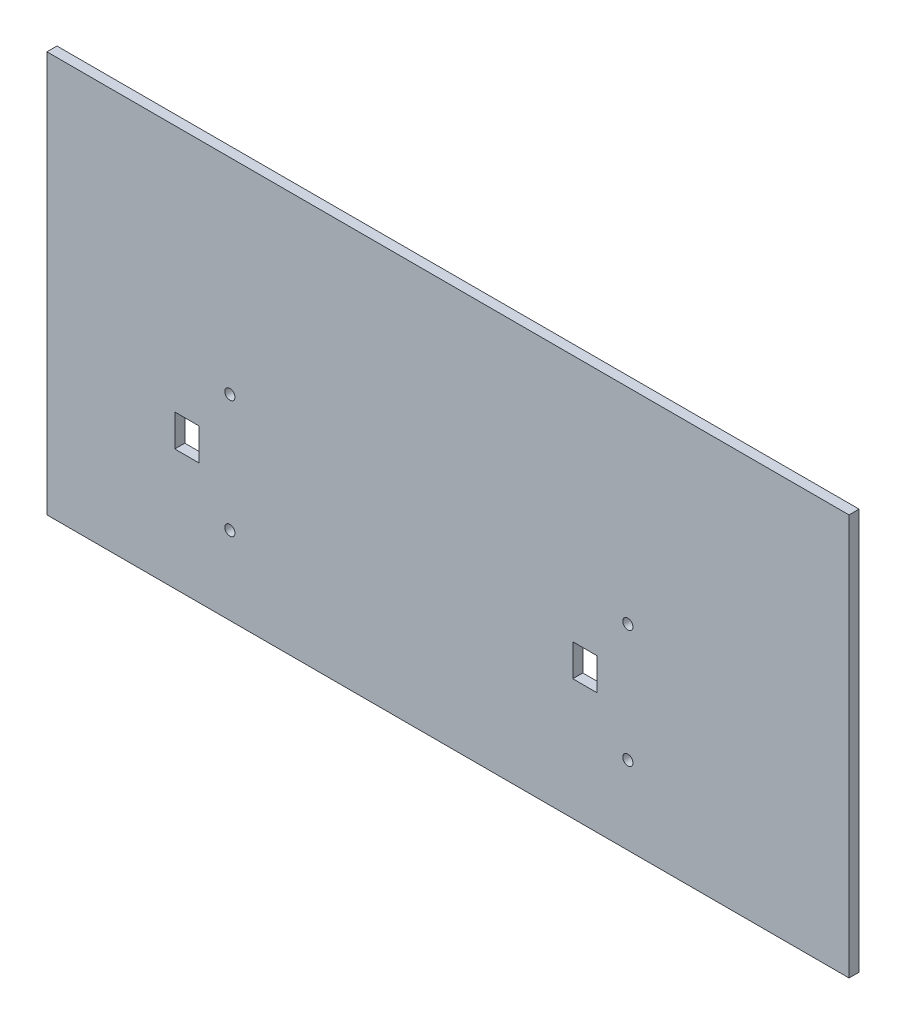
SolidWorks part; units mm, degrees
ref_plane "Front Plane" through (0, 0, 0) normal (0, 0, 1) x (1, 0, 0)
ref_plane "Top Plane" through (0, 0, 0) normal (0, 1, 0) x (1, 0, 0)
ref_plane "Right Plane" through (0, 0, 0) normal (1, 0, 0) x (0, 0, -1)
sketch "Sketch1" plane through (0, 0, 0) normal (0, 0, 1) x (1, 0, 0)
  line L1 (-127, -63.5) -> (127, -63.5)
  line L2 (-127, -63.5) -> (-127, 63.5)
  line L3 (-127, 63.5) -> (127, 63.5)
  line L4 (127, -63.5) -> (127, 63.5)
  line L5 (-127, -63.5) -> (127, 63.5) construction
  line L6 (-127, 63.5) -> (127, -63.5) construction
  point P0 (0, 0)
  dimension "D1" = 254
  dimension "D2" = 127
extrude "Boss-Extrude1" add sketch "Sketch1" along normal mid plane 3.175
sketch "Sketch3" plane through (0, 0, -1.5875) normal (0, 0, -1) x (-1, 0, 0)
  line L0 (-47.13, -15.025) -> (-47.13, -25.175)
  line L1 (-47.13, -15.025) -> (-39.51, -15.025)
  line L2 (-47.13, -25.175) -> (-39.51, -25.175)
  line L3 (-39.51, -15.025) -> (-39.51, -25.175)
  line L4 (78.8945, -15.025) -> (78.8945, -25.175)
  line L5 (78.8945, -15.025) -> (86.5145, -15.025)
  line L6 (78.8945, -25.175) -> (86.5145, -25.175)
  line L7 (86.5145, -15.025) -> (86.5145, -25.175)
  circle A0 centre (-56.955, -1.46) radius 1.61
  circle A1 centre (-56.955, -38.74) radius 1.61
  circle A2 centre (69.0695, -38.74) radius 1.61
  circle A3 centre (69.0695, -1.46) radius 1.61
  dimension "D1" = 3.22
  dimension "D2" = 7.62
  dimension "D3" = 7.62
extrude "Cut-Extrude2" cut sketch "Sketch3" against normal blind 5.08
